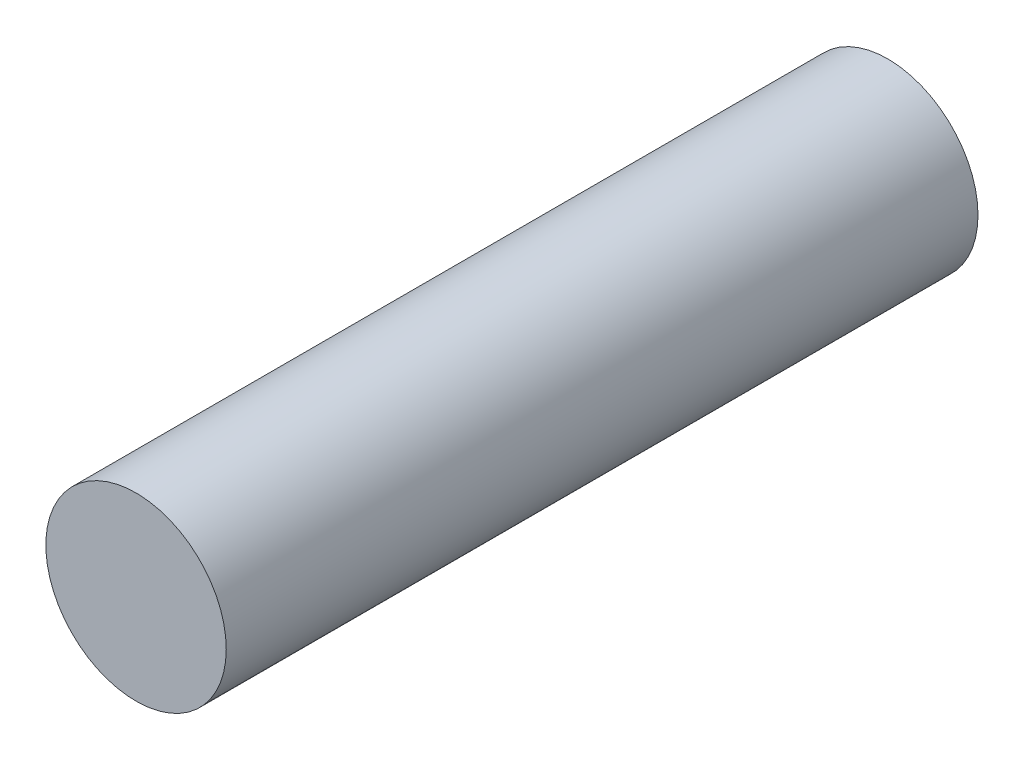
SolidWorks part; units mm, degrees
ref_plane "Front Plane" through (0, 0, 0) normal (0, 0, 1) x (1, 0, 0)
ref_plane "Top Plane" through (0, 0, 0) normal (0, 1, 0) x (1, 0, 0)
ref_plane "Right Plane" through (0, 0, 0) normal (1, 0, 0) x (0, 0, -1)
sketch "Sketch1" plane through (0, 0, 0) normal (0, 0, 1) x (1, 0, 0)
  circle A0 centre (0, 0) radius 3
  dimension "D1" = 6
extrude "Boss-Extrude1" add sketch "Sketch1" along normal blind 25
